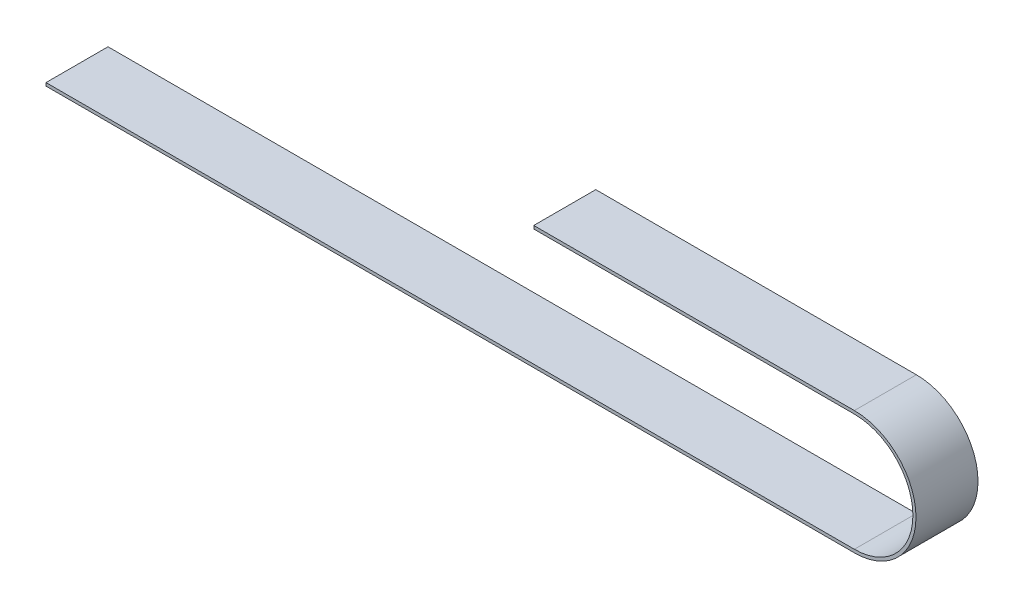
SolidWorks part; units mm, degrees
ref_plane "Front Plane" through (0, 0, 0) normal (0, 0, 1) x (1, 0, 0)
ref_plane "Top Plane" through (0, 0, 0) normal (0, 1, 0) x (1, 0, 0)
ref_plane "Right Plane" through (0, 0, 0) normal (1, 0, 0) x (0, 0, -1)
sketch "Sketch1" plane through (0, 0, 0) normal (0, 0, 1) x (1, 0, 0)
  line L0 (0, 55) -> (521.4472, 55)
  line L1 (0, 60) -> (0, 50) construction
  line L2 (521.4472, 132.5) -> (314.6312, 132.5)
  line L3 (314.6312, 127.5) -> (314.6312, 137.5) construction
  arc A0 (521.4472, 55) -> (521.4472, 132.5) centre (521.4472, 93.75) ccw
  dimension "D1" = 850
extrude "Extrude-Thin1" add sketch "Sketch1" against normal blind 40 from offset 5 thin contours L0 A0 L2 thin type mid plane wall 2 offset against normal yes
